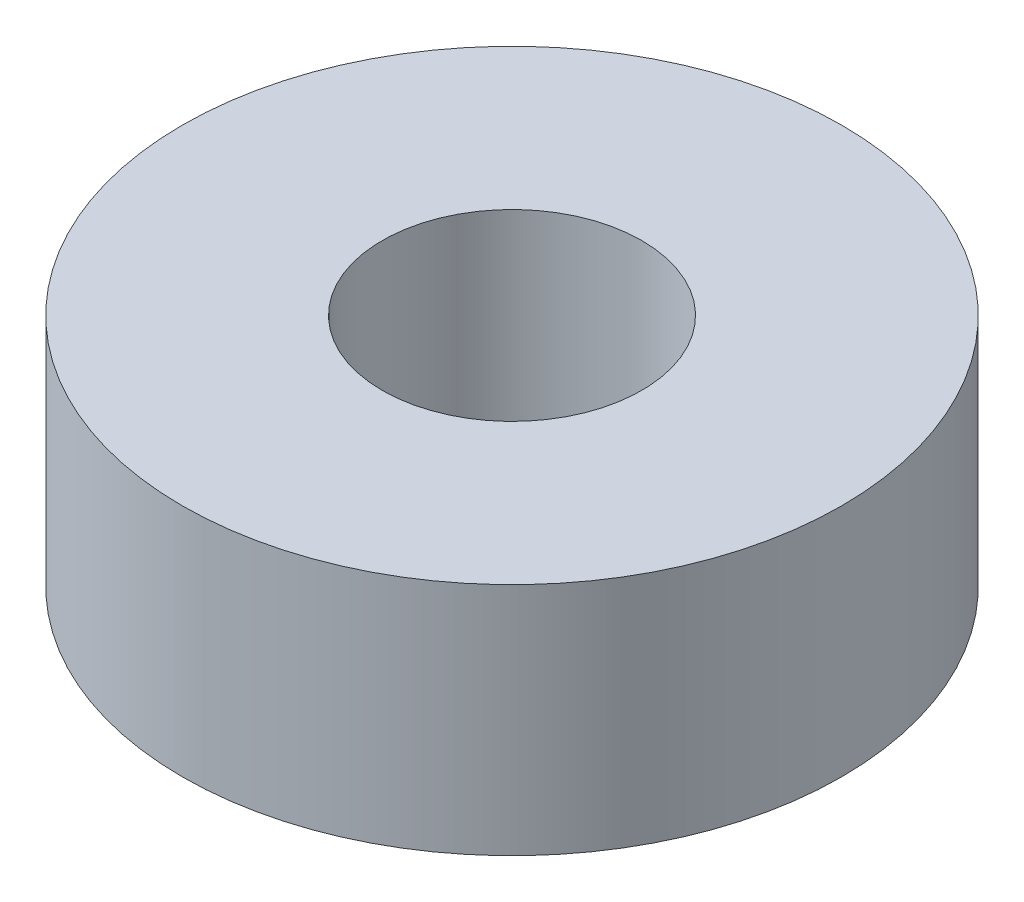
SolidWorks part; units mm, degrees
ref_plane "Front Plane" through (0, 0, 0) normal (0, 0, 1) x (1, 0, 0)
ref_plane "Top Plane" through (0, 0, 0) normal (0, 1, 0) x (1, 0, 0)
ref_plane "Right Plane" through (0, 0, 0) normal (1, 0, 0) x (0, 0, -1)
sketch "Sketch1" plane through (0, 0, 0) normal (0, 1, 0) x (1, 0, 0)
  circle A0 centre (0, 0) radius 2.5
  circle A1 centre (0, 0) radius 6.35
  dimension "D1" = 5
  dimension "D2" = 12.7
extrude "Boss-Extrude1" add sketch "Sketch1" along normal blind 4.5212
